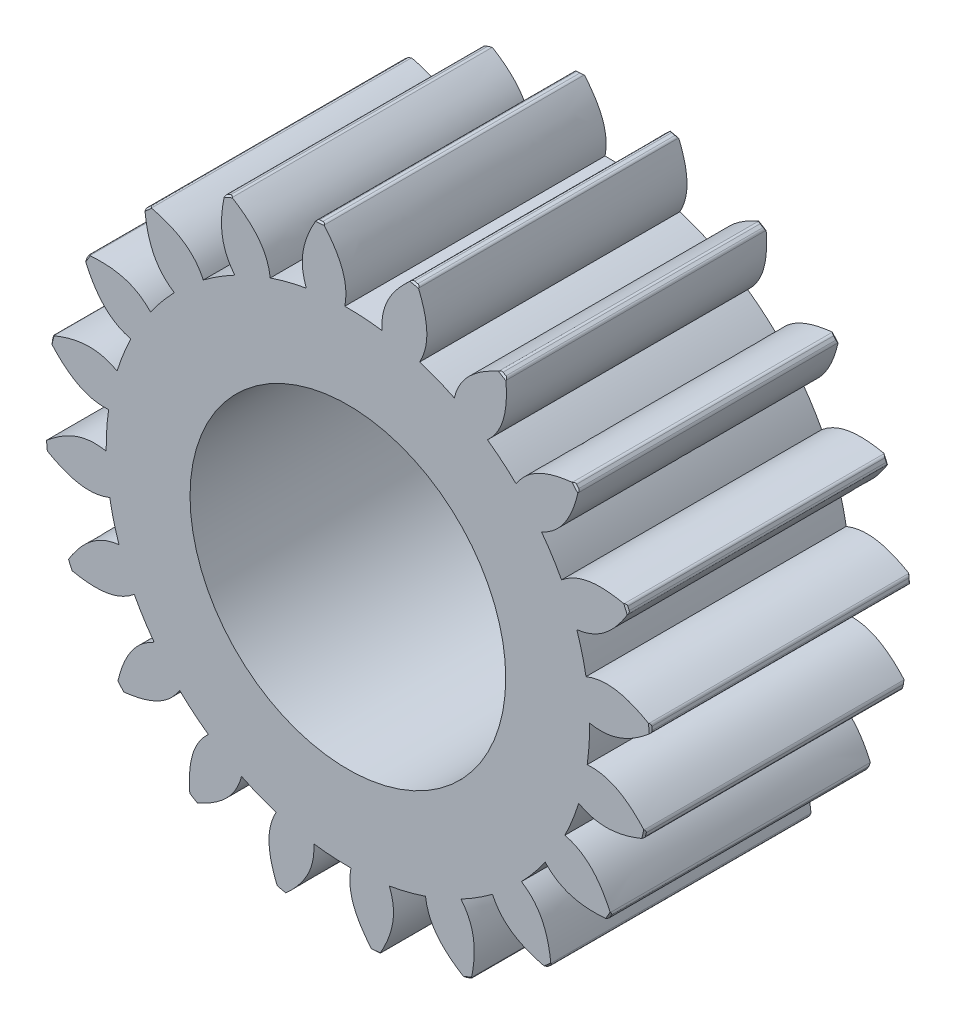
SolidWorks part; units mm, degrees
ref_plane "Front Plane" through (0, 0, 0) normal (0, 0, 1) x (1, 0, 0)
ref_plane "Top Plane" through (0, 0, 0) normal (0, 1, 0) x (1, 0, 0)
ref_plane "Right Plane" through (0, 0, 0) normal (1, 0, 0) x (0, 0, -1)
sketch "Sketch1" plane through (0, 0, 0) normal (0, 0, 1) x (1, 0, 0)
  line L0 (-5.7131, 31.8669) -> (-2.9657, 31.8857) construction
  line L1 (5.2766, 31.9421) -> (15.6583, 28.3365) construction
  line L2 (15.6583, 28.3365) -> (24.2357, 21.4656) construction
  line L3 (24.2357, 21.4656) -> (30.0203, 12.1212) construction
  line L4 (5.2766, 31.9421) -> (-5.7134, 33.7576) construction
  line L5 (15.6583, 28.3365) -> (-3.5798, 38.9672) construction
  line L6 (24.2357, 21.4656) -> (2.3756, 46.1467) construction
  line L7 (30.0203, 12.1212) -> (13.5617, 52.8839) construction
  line L8 (0, 0) -> (-0.2095, 30.6243) construction
  line L10 (0, 0) -> (-2.9657, 31.8857) construction
  circle A0 centre (0, 0) radius 32.375
  circle A1 centre (0, 0) radius 30.625
  circle A2 centre (0, 0) radius 35 construction
  circle A3 centre (0, 0) radius 38.5
  spline S0 degree 3 poles (-5.2628, 30.1694) (-5.492, 30.7439) (-5.8056, 31.9615) (-5.7736, 35.0157) (-1.0569, 44.2495) (6.3297, 50.2113) (13.5617, 52.8839) knots -0.054886 -0.054886 -0.054886 -0.054886 0 0.063219 0.251459 1 1 1 1
  spline S1 degree 3 poles (-0.3914, 30.6225) (-0.272, 31.2294) (-0.1884, 32.484) (-0.7832, 35.4799) (-7.1218, 43.6854) (-15.4812, 48.1827) (-23.0821, 49.4756) knots -0.054886 -0.054886 -0.054886 -0.054886 0 0.063219 0.251459 1 1 1 1
  dimension "D1" = 77
  dimension "D2" = 70
  dimension "D3" = 64.75
  dimension "D4" = 61.25
  dimension "D5" = 10.99
  dimension "D6" = 10.99
  dimension "D7" = 21.98
  dimension "D8" = 32.97
  dimension "D9" = 43.96
extrude "Boss-Extrude1" add sketch "Sketch1" along normal blind 32.97 contours A1 | A0 S1 A3 S0 | A1 S1 A0 S0
chamfer "Chamfer1" distance 0.2 angle 45 2 edges at (-3.5655, 38.3345, 0) (-3.5655, 38.3345, 32.97)
fillet "Fillet1" radius 0.4 2 edges at (-3.9848, 38.2932, 16.485) (-3.1457, 38.3713, 16.485)
pattern_circular "CirPattern1" count 20 over 360 about axis through (0, 0, 32.97) along (0, 0, 1) of "Boss-Extrude1", "Chamfer1", "Fillet1"
sketch "Sketch2" plane through (0, 0, 32.97) normal (0, 0, 1) x (1, 0, 0)
  circle A0 centre (0, 0) radius 20
  dimension "D1" = 40
extrude "Cut-Extrude1" cut sketch "Sketch2" against normal through all
